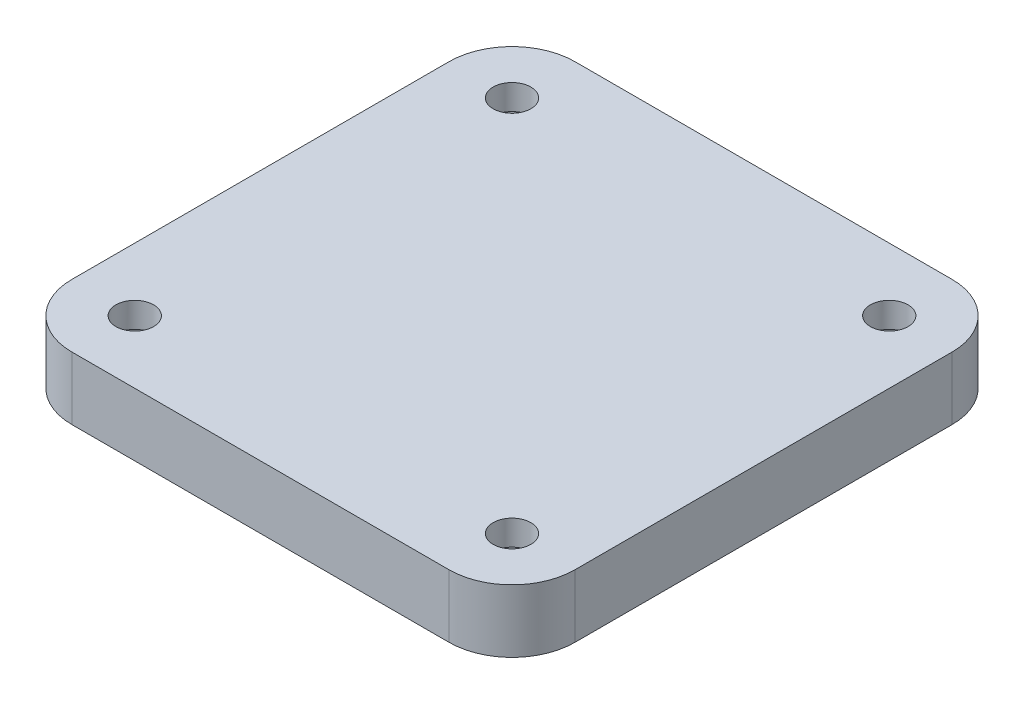
SolidWorks part; units mm, degrees
ref_plane "前视基准面" through (0, 0, 0) normal (0, 0, 1) x (1, 0, 0)
ref_plane "上视基准面" through (0, 0, 0) normal (0, 1, 0) x (1, 0, 0)
ref_plane "右视基准面" through (0, 0, 0) normal (1, 0, 0) x (0, 0, -1)
sketch "草图1" plane through (0, 0, 0) normal (0, 1, 0) x (1, 0, 0)
  line L0 (0, -8.5292) -> (0, -13.8192) construction
  line L1 (-20, 20) -> (20, 20)
  line L2 (-20, 20) -> (-20, -20)
  line L3 (-20, -20) -> (20, -20)
  line L4 (20, 20) -> (20, -20)
  line L5 (-20, 20) -> (20, -20) construction
  line L6 (-20, -20) -> (20, 20) construction
  line L7 (17.3893, 0) -> (25.5762, 0) construction
  point P0 (0, 0)
  dimension "D1" = 40
  dimension "D2" = 40
extrude "凸台-拉伸1" add sketch "草图1" along normal blind 5
sketch "草图2" plane through (0, 5, 0) normal (0, 1, 0) x (1, 0, 0)
  line L0 (0, -2.064) -> (0, -4.4472) construction
  line L1 (4.4259, 0) -> (7.9156, 0) construction
  circle A0 centre (-15, 15) radius 1.5
  circle A1 centre (15, 15) radius 1.5
  circle A2 centre (15, -15) radius 1.5
  circle A3 centre (-15, -15) radius 1.5
  circle A4 centre (-15, 15) radius 3
  circle A5 centre (15, 15) radius 3
  circle A6 centre (15, -15) radius 3
  circle A7 centre (-15, -15) radius 3
  dimension "D1" = 3
  dimension "D2" = 30
  dimension "D3" = 30
  dimension "D4" = 6
extrude "切除-拉伸1" cut sketch "草图2" against normal blind 10 contours A0 | A1 | A2 | A3
fillet "圆角1" radius 5 4 edges at (20, 2.5, 20) (20, 2.5, -20) (-20, 2.5, 20) (-20, 2.5, -20)
sketch "草图4" plane through (0, 0, 0) normal (0, -1, 0) x (1, 0, 0)
  line L0 (0, -2.4051) -> (0, -5.9989) construction
  line L1 (5.8054, 0) -> (11.4449, 0) construction
  line L2 (12.25, 16.5877) -> (15, 18.1754)
  line L3 (-15, 18.1754) -> (-17.75, 16.5877)
  line L4 (-17.75, 16.5877) -> (-17.75, 13.4123)
  line L5 (-17.75, 13.4123) -> (-15, 11.8246)
  line L6 (-15, 11.8246) -> (-12.25, 13.4123)
  line L7 (-12.25, 13.4123) -> (-12.25, 16.5877)
  line L8 (-12.25, 16.5877) -> (-15, 18.1754)
  line L9 (12.25, 13.4123) -> (12.25, 16.5877)
  line L10 (15, 11.8246) -> (12.25, 13.4123)
  line L11 (17.75, 13.4123) -> (15, 11.8246)
  line L12 (17.75, 16.5877) -> (17.75, 13.4123)
  line L13 (15, 18.1754) -> (17.75, 16.5877)
  line L14 (12.25, -13.4123) -> (12.25, -16.5877)
  line L15 (15, -11.8246) -> (12.25, -13.4123)
  line L16 (17.75, -13.4123) -> (15, -11.8246)
  line L17 (17.75, -16.5877) -> (17.75, -13.4123)
  line L18 (15, -18.1754) -> (17.75, -16.5877)
  line L19 (12.25, -16.5877) -> (15, -18.1754)
  line L20 (-12.25, -16.5877) -> (-15, -18.1754)
  line L21 (-12.25, -13.4123) -> (-12.25, -16.5877)
  line L22 (-15, -11.8246) -> (-12.25, -13.4123)
  line L23 (-17.75, -13.4123) -> (-15, -11.8246)
  line L24 (-17.75, -16.5877) -> (-17.75, -13.4123)
  line L25 (-15, -18.1754) -> (-17.75, -16.5877)
  circle A0 centre (-15, 15) radius 2.75 construction
  dimension "D1" = 5.5
extrude "切除-拉伸3" cut sketch "草图4" against normal blind 3
